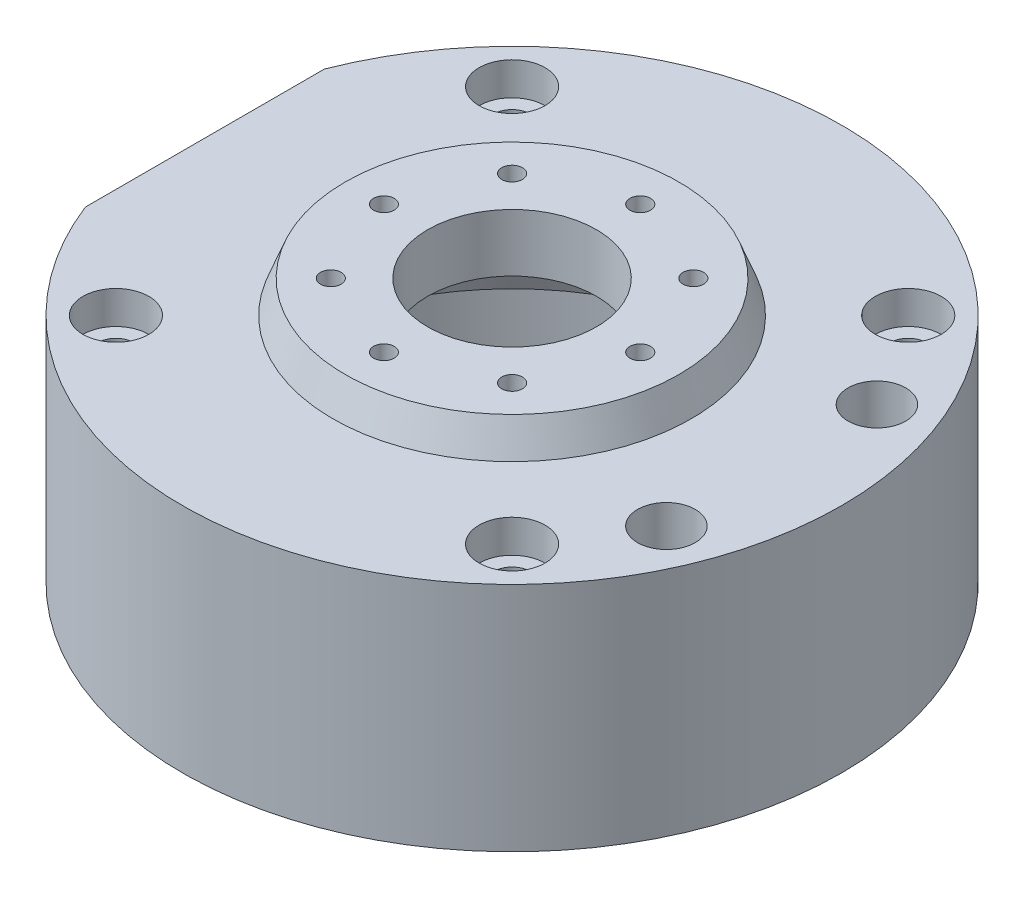
SolidWorks part; units mm, degrees
ref_plane "Front Plane" through (0, 0, 0) normal (0, 0, 1) x (1, 0, 0)
ref_plane "Top Plane" through (0, 0, 0) normal (0, 1, 0) x (1, 0, 0)
ref_plane "Right Plane" through (0, 0, 0) normal (1, 0, 0) x (0, 0, -1)
sketch "Sketch1" plane through (0, 0, 0) normal (0, 0, 1) x (1, 0, 0)
  line L0 (0, 10.5736) -> (0, -6.4838) construction
  line L1 (10.235, 32) -> (10.235, 25)
  line L2 (10.235, 25) -> (25, 25)
  line L3 (25, 25) -> (29.55, 10)
  line L4 (29.55, 10) -> (29.55, 0)
  line L5 (29.55, 0) -> (40, 0)
  line L6 (40, 0) -> (40, 28.1)
  line L7 (40, 28.1) -> (21.75, 28.1)
  line L8 (21.75, 28.1) -> (20.25, 32)
  line L9 (20.25, 32) -> (10.235, 32)
  dimension "D1" = 80
  dimension "D2" = 59.1
  dimension "D3" = 10
  dimension "D4" = 50
  dimension "D5" = 25
  dimension "D6" = 28.1
  dimension "D7" = 32
  dimension "D8" = 20.47
  dimension "D9" = 40.5
  dimension "D10" = 43.5
revolve "Revolve1" add sketch "Sketch1" angle 360 about L0
sketch "Sketch2" plane through (0, 28.1, 0) normal (0, 1, 0) x (1, 0, 0)
  line L1 (24.0416, -24.0416) -> (-24.0416, -24.0416) construction
  line L2 (24.0416, -24.0416) -> (24.0416, 24.0416) construction
  line L3 (24.0416, 24.0416) -> (-24.0416, 24.0416) construction
  line L4 (-24.0416, -24.0416) -> (-24.0416, 24.0416) construction
  line L5 (24.0416, -24.0416) -> (-24.0416, 24.0416) construction
  line L6 (24.0416, 24.0416) -> (-24.0416, -24.0416) construction
  point P0 (0, 0)
  dimension "D1" = 68
hole_wizard "CBORE for M4 SHCS1" positions "Sketch3" profile "Sketch4" counterbore size "M4" standard "ANSI Metric" end condition through all
sketch "Sketch3" plane through (0, 28.1, 0) normal (0, 1, 0) x (1, 0, 0)
  point P0 (-24.0416, 24.0416)
  point P3 (24.0416, 24.0416)
  point P6 (24.0416, -24.0416)
  point P9 (-24.0416, -24.0416)
sketch "Sketch4" plane through (-24.0416, 28.1, -24.0416) normal (1, 0, 0) x (0, 0, 1)
  line L0 (0, 0) -> (0, 28.1)
  line L1 (0, 28.1) -> (2.25, 28.1)
  line L3 (2.25, 28.1) -> (2.25, 4)
  line L4 (2.25, 4) -> (4, 4)
  line L5 (4, 4) -> (4, 0)
  line L7 (4, 0) -> (0, 0)
  line L11 (0, -6.35) -> (0, 107.95) construction
  dimension "Thru Hole Dia." = 4.5
  dimension "Thru Hole Depth" = 28.1
  dimension "C'Bore Dia." = 8
  dimension "C'Bore Depth" = 4
sketch "Sketch5" plane through (0, 32, 0) normal (0, 1, 0) x (1, 0, 0)
  line L0 (0, -15.5563) -> (15.5563, 0) construction
  line L1 (11, -11) -> (-11, -11) construction
  line L2 (11, -11) -> (11, 11) construction
  line L3 (11, 11) -> (-11, 11) construction
  line L4 (-11, -11) -> (-11, 11) construction
  line L5 (11, -11) -> (-11, 11) construction
  line L6 (11, 11) -> (-11, -11) construction
  line L7 (0, -15.5563) -> (-15.5563, 0) construction
  line L8 (15.5563, 0) -> (0, 15.5563) construction
  line L9 (-15.5563, 0) -> (0, 15.5563) construction
  line L10 (0, -15.5563) -> (0, 15.5563) construction
  line L11 (15.5563, 0) -> (-15.5563, 0) construction
  point P0 (0, 0)
  point P7 (0, 0)
  dimension "D1" = 22
hole_wizard "M3x0.5 Tapped Hole1" positions "Sketch6" profile "Sketch7" tap size "M3x0.5" standard "ANSI Metric" end condition through all
sketch "Sketch6" plane through (0, 32, 0) normal (0, 1, 0) x (1, 0, 0)
  point P0 (-11, 11)
  point P3 (11, 11)
  point P6 (11, -11)
  point P9 (-11, -11)
  point P12 (0, 15.5563)
  point P15 (15.5563, 0)
  point P18 (0, -15.5563)
  point P21 (-15.5563, 0)
sketch "Sketch7" plane through (-11, 32, -11) normal (1, 0, 0) x (0, 0, 1)
  line L0 (0, 0) -> (0, 32)
  line L1 (0, 32) -> (1.25, 32)
  line L2 (1.25, 32) -> (1.25, 0)
  line L5 (1.25, 0) -> (0, 0)
  line L11 (0, -6.35) -> (0, 107.95) construction
  dimension "Thru Tap Drill Dia." = 2.5
  dimension "Thru Tap Drill Depth" = 32
cosmetic thread "Hole Thread1" parameters "D2"=3
cosmetic thread "Hole Thread2" parameters "D2"=3
cosmetic thread "Hole Thread3" parameters "D2"=3
cosmetic thread "Hole Thread4" parameters "D2"=3
cosmetic thread "Hole Thread11" parameters "D2"=3
cosmetic thread "Hole Thread12" parameters "D2"=3
cosmetic thread "Hole Thread13" parameters "D2"=3
cosmetic thread "Hole Thread14" parameters "D2"=3
sketch "Sketch8" plane through (0, 28.1, 0) normal (0, 1, 0) x (1, 0, 0)
  line L0 (0, 0) -> (31.5087, 12.775)
  line L1 (31.5087, 12.775) -> (31.5087, -12.775)
  line L2 (31.5087, -12.775) -> (0, 0)
  line L3 (31.5087, -12.775) -> (37.0691, -15.0294)
  circle A0 centre (0, 0) radius 40 construction
  dimension "D1" = 25.55
  dimension "D2" = 6
hole_wizard "M8x1.0 Tapped Hole1" positions "Sketch9" profile "Sketch10" tap size "M8x1.0" standard "ANSI Metric"
sketch "Sketch9" plane through (0, 28.1, 0) normal (0, 1, 0) x (1, 0, 0)
  point P0 (31.5087, 12.775)
  point P3 (31.5087, -12.775)
cosmetic thread "Hole Thread5" parameters "D1"=16, "D2"=8
cosmetic thread "Hole Thread6" parameters "D1"=16, "D2"=8
sketch "Sketch10" plane through (31.5087, 28.1, -12.775) normal (1, 0, 0) x (0, 0, 1)
  line L0 (0, 0) -> (0, 23.103)
  line L1 (0, 23.103) -> (3.5, 21)
  line L2 (3.5, 21) -> (3.5, 0)
  line L5 (3.5, 0) -> (0, 0)
  line L10 (0, 23.103) -> (-3.5, 21) construction
  line L11 (0, -6.35) -> (0, 107.95) construction
  dimension "Tap Drill Dia." = 7
  dimension "Tap Drill Depth" = 21
  dimension "Drill Angle" = 118
hole_wizard "Hole1" positions "Sketch11" profile "Sketch12" legacy end condition through all
sketch "Sketch11" plane through (0, 0, 0) normal (0, -1, 0) x (-1, 0, 0)
  point P0 (-31.5087, -12.775)
  point P3 (-31.5087, 12.775)
sketch "Sketch12" plane through (31.5087, 0, 12.775) normal (1, 0, 0) x (0, 0, -1)
  line L0 (0, 0) -> (0, 32)
  line L1 (0, 32) -> (2.2, 32)
  line L2 (2.2, 32) -> (2.2, 1.27)
  line L3 (2.2, 1.27) -> (3.925, 1.27)
  line L4 (3.925, 1.27) -> (3.925, 0)
  line L5 (3.925, 0) -> (0, 0)
  line L6 (0, 110) -> (0, -10) construction
  dimension "Diameter" = 4.4
  dimension "Depth" = 32
  dimension "C-Bore Diameter" = 7.85
  dimension "C-Bore Depth" = 1.27
sketch "Sketch13" plane through (0, 0, 0) normal (0, -1, 0) x (1, 0, 0)
  line L0 (-37.2794, 14.5) -> (-37.2794, -14.5)
  circle A0 centre (0, 0) radius 40 construction
  arc A1 (-37.2794, 14.5) -> (-37.2794, -14.5) centre (0, 0) ccw
  dimension "D1" = 29
extrude "Cut-Extrude1" cut sketch "Sketch13" against normal through all and the other way through all
sketch "Sketch14" plane through (-37.2794, 0, 0) normal (-1, 0, 0) x (0, 0, 1)
  line L0 (0, 0) -> (14.5, 0) construction
  line L1 (-14.5, 0) -> (14.5, 0) construction
  line L2 (0, 0) -> (0, 14.5) construction
  line L3 (-7, 7.3586) -> (-7, 0)
  line L4 (11, 3.5) -> (-11, 3.5) construction
  line L5 (11, 3.5) -> (11, 25.5) construction
  line L6 (11, 25.5) -> (-11, 25.5) construction
  line L7 (-11, 3.5) -> (-11, 25.5) construction
  line L8 (11, 3.5) -> (-11, 25.5) construction
  line L9 (11, 25.5) -> (-11, 3.5) construction
  line L10 (-7, 0) -> (7, 0)
  line L11 (7, 0) -> (7, 7.3586)
  arc A0 (7, 7.3586) -> (-7, 7.3586) centre (0, 14.5) ccw
  dimension "D3" = 10
  dimension "D1" = 22
  dimension "D2" = 14
extrude "Cut-Extrude2" cut sketch "Sketch14" against normal up to next
hole_wizard "M3x0.5 Tapped Hole2" positions "Sketch15" profile "Sketch16" tap size "M3x0.5" standard "ANSI Metric"
sketch "Sketch15" plane through (-37.2794, 0, 0) normal (-1, 0, 0) x (0, 0, 1)
  point P0 (-11, 25.5)
  point P3 (-11, 3.5)
  point P6 (11, 3.5)
  point P9 (11, 25.5)
sketch "Sketch16" plane through (-37.2794, 25.5, -11) normal (0, 1, 0) x (0, 0, 1)
  line L0 (0, 0) -> (0, 8.2511)
  line L1 (0, 8.2511) -> (1.25, 7.5)
  line L2 (1.25, 7.5) -> (1.25, 0)
  line L5 (1.25, 0) -> (0, 0)
  line L10 (0, 8.2511) -> (-1.25, 7.5) construction
  line L11 (0, -6.35) -> (0, 107.95) construction
  dimension "Tap Drill Dia." = 2.5
  dimension "Tap Drill Depth" = 7.5
  dimension "Drill Angle" = 118
cosmetic thread "Hole Thread7" parameters "D1"=6, "D2"=3
cosmetic thread "Hole Thread8" parameters "D1"=6, "D2"=3
cosmetic thread "Hole Thread9" parameters "D1"=6, "D2"=3
cosmetic thread "Hole Thread10" parameters "D1"=6, "D2"=3
